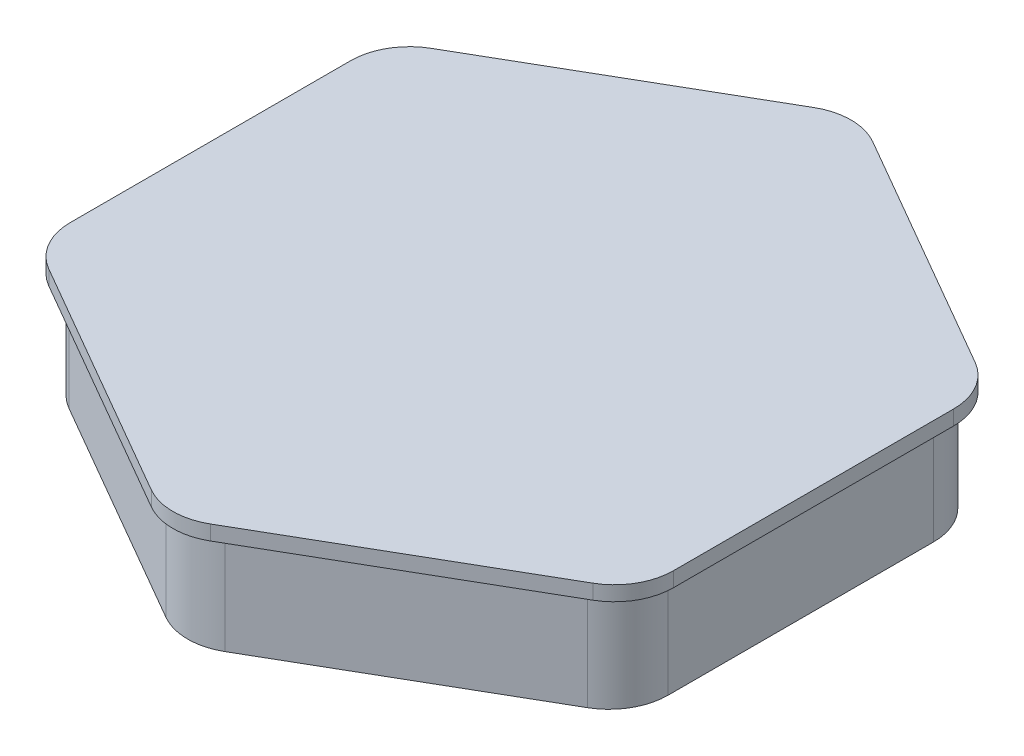
SolidWorks part; units mm, degrees
material "Thornel VCB-20 Carbon Cloth"
ref_plane "Front Plane" through (0, 0, 0) normal (0, 0, 1) x (1, 0, 0)
ref_plane "Top Plane" through (0, 0, 0) normal (0, 1, 0) x (1, 0, 0)
ref_plane "Right Plane" through (0, 0, 0) normal (1, 0, 0) x (0, 0, -1)
sketch "Sketch2" plane through (0, 0, 0) normal (0, 1, 0) x (1, 0, 0)
  line L1 (-10, 107.3205) -> (-87.9423, 62.3205)
  line L2 (-97.9423, 45) -> (-97.9423, -45)
  line L3 (-87.9423, -62.3205) -> (-10, -107.3205)
  line L4 (10, -107.3205) -> (87.9423, -62.3205)
  line L5 (97.9423, -45) -> (97.9423, 45)
  line L6 (87.9423, 62.3205) -> (10, 107.3205)
  circle A0 centre (0, 0) radius 97.9423 construction
  arc A1 (97.9423, 45) -> (87.9423, 62.3205) centre (77.9423, 45) ccw
  arc A2 (87.9423, -62.3205) -> (97.9423, -45) centre (77.9423, -45) ccw
  arc A3 (-10, -107.3205) -> (10, -107.3205) centre (0, -90) ccw
  arc A4 (-97.9423, -45) -> (-87.9423, -62.3205) centre (-77.9423, -45) ccw
  arc A5 (-87.9423, 62.3205) -> (-97.9423, 45) centre (-77.9423, 45) ccw
  arc A6 (-10, 107.3205) -> (10, 107.3205) centre (0, 90) cw
  dimension "D1" = 20
  dimension "D2" = 90
extrude "Boss-Extrude2" add sketch "Sketch2" along normal blind 35
sketch "Sketch5" plane through (0, 35, 0) normal (0, 1, 0) x (1, 0, 0)
  line L1 (-10, 112.3205) -> (-92.2724, 64.8205)
  line L2 (-102.2724, 47.5) -> (-102.2724, -47.5)
  line L3 (-92.2724, -64.8205) -> (-10, -112.3205)
  line L4 (10, -112.3205) -> (92.2724, -64.8205)
  line L5 (102.2724, -47.5) -> (102.2724, 47.5)
  line L6 (92.2724, 64.8205) -> (10, 112.3205)
  circle A0 centre (0, 0) radius 102.2724 construction
  arc A1 (102.2724, 47.5) -> (92.2724, 64.8205) centre (82.2724, 47.5) ccw
  arc A2 (92.2724, -64.8205) -> (102.2724, -47.5) centre (82.2724, -47.5) ccw
  arc A3 (-10, -112.3205) -> (10, -112.3205) centre (0, -95) ccw
  arc A4 (-102.2724, -47.5) -> (-92.2724, -64.8205) centre (-82.2724, -47.5) ccw
  arc A5 (-92.2724, 64.8205) -> (-102.2724, 47.5) centre (-82.2724, 47.5) ccw
  arc A6 (-10, 112.3205) -> (10, 112.3205) centre (0, 95) cw
  dimension "D1" = 20
  dimension "D2" = 95
extrude "Boss-Extrude3" add sketch "Sketch5" along normal blind 5
scale "Scale1" scale about centroid uniform scaling yes scale factor 0.3
